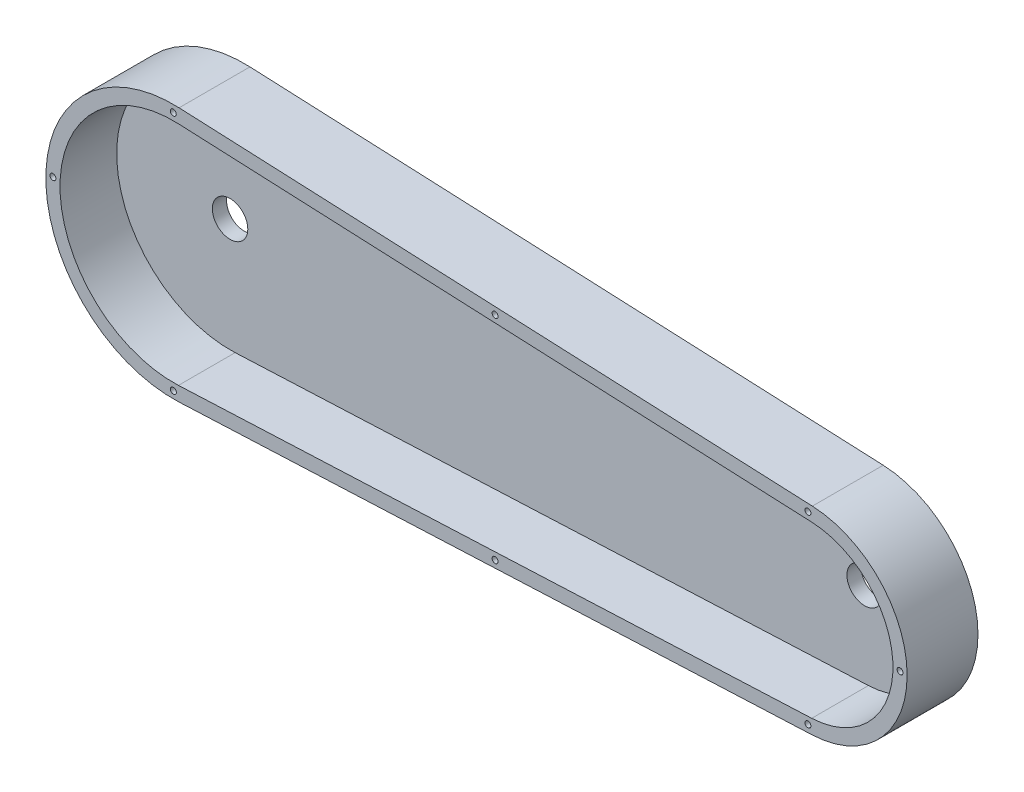
SolidWorks part; units mm, degrees
ref_plane "Front Plane" through (0, 0, 0) normal (0, 0, 1) x (1, 0, 0)
ref_plane "Top Plane" through (0, 0, 0) normal (0, 1, 0) x (1, 0, 0)
ref_plane "Right Plane" through (0, 0, 0) normal (1, 0, 0) x (0, 0, -1)
sketch "Sketch1" plane through (0, 0, 0) normal (0, 0, 1) x (1, 0, 0)
  line L0 (-71.0013, 89.9102) -> (375.8187, 69.9301)
  line L1 (-71.0013, -89.9102) -> (375.8187, -69.9301)
  line L2 (-71.0013, 0) -> (375.8187, 0) construction
  arc A0 (-71.0013, 89.9102) -> (-71.0013, -89.9102) centre (-75.0217, 0) ccw
  arc A1 (375.8187, 69.9301) -> (375.8187, -69.9301) centre (372.6917, 0) cw
  dimension "D1" = 90
  dimension "D2" = 70
  dimension "D3" = 446.82
extrude "Boss-Extrude2" add sketch "Sketch1" along normal blind 50
shell "Shell2" thickness 10
sketch "Sketch2" plane through (0, 0, 10) normal (0, 0, 1) x (1, 0, 0)
  circle A0 centre (-75.0217, 0) radius 12.5
  circle A1 centre (372.6917, 0) radius 12.5
  dimension "D1" = 25
  dimension "D2" = 25
extrude "Cut-Extrude1" cut sketch "Sketch2" against normal blind 10
hole_wizard "M5 Tapped Hole1" positions "Sketch4" profile "Sketch3" tap size "M5" standard "ISO"
sketch "Sketch4" plane through (0, 0, 50) normal (0, 0, 1) x (1, 0, 0)
  line L4 (375.8187, 69.9301) -> (-71.0013, 89.9102) construction
  line L5 (-71.0013, -89.9102) -> (375.8187, -69.9301) construction
  arc A1 (-71.0013, 89.9102) -> (-71.0013, -89.9102) centre (-75.0217, 0) ccw construction
  point P0 (-160.0217, 3.1339)
  point P1 (-75.0813, 85)
  point P3 (-75.0217, -85)
  point P5 (437.6917, 0)
  point P7 (372.6861, -65)
  point P9 (372.6917, 65)
  point P23 (-165.0217, 0)
  point P47 (151.962, 74.9201)
  point P49 (151.9629, -74.9401)
  point P59 (152.4087, 79.9201)
  point P62 (152.4087, -79.9201)
  dimension "D1" = 5
  dimension "D2" = 85
  dimension "D3" = 5
  dimension "D4" = 5
  dimension "D5" = 65
  dimension "D6" = 65
  dimension "D7" = 65
  dimension "D10" = 85
sketch "Sketch3" plane through (-160.0217, 3.1339, 50) normal (1, 0, 0) x (0, -1, 0)
  line L0 (0, 0) -> (0, 11.2618)
  line L1 (0, 11.2618) -> (2.1, 10)
  line L2 (2.1, 10) -> (2.1, 0)
  line L5 (2.1, 0) -> (0, 0)
  line L10 (0, 11.2618) -> (-2.1, 10) construction
  line L11 (0, -6.35) -> (0, 107.95) construction
  dimension "Tap Drill Dia." = 4.2
  dimension "Tap Drill Depth" = 10
  dimension "Drill Angle" = 118
cosmetic thread "Hole Thread1" parameters "D1"=10, "D2"=5
cosmetic thread "Hole Thread2" parameters "D1"=10, "D2"=5
cosmetic thread "Hole Thread3" parameters "D1"=10, "D2"=5
cosmetic thread "Hole Thread4" parameters "D1"=10, "D2"=5
cosmetic thread "Hole Thread5" parameters "D1"=10, "D2"=5
cosmetic thread "Hole Thread6" parameters "D1"=10, "D2"=5
cosmetic thread "Hole Thread7" parameters "D1"=10, "D2"=5
cosmetic thread "Hole Thread8" parameters "D1"=10, "D2"=5
sketch "Sketch5" plane through (0, 0, 0) normal (0, 0, -1) x (-1, 0, 0)
  line L0 (-372.6917, 0) -> (75.0217, 0) construction
sketch "Sketch7" plane through (0, 0, 0) normal (0, 0, -1) x (-1, 0, 0)
  line L0 (-270.4474, 4.605) -> (-111.9727, -17.4354) construction
  line L1 (-268.2215, -5.8009) -> (-109.8269, -27.8301)
  line L2 (-268.2215, -5.8009) -> (-291.6342, -2.5447)
  line L3 (-291.6342, -2.5447) -> (-288.8792, 17.2647)
  line L4 (-288.8792, 17.2647) -> (-90.7858, -10.2858)
  line L5 (-90.7858, -10.2858) -> (-93.5409, -30.0951)
  line L6 (-93.5409, -30.0951) -> (-109.8269, -27.8301)
  circle A0 centre (-270.4474, 4.605) radius 2.5
  circle A1 centre (-191.21, -6.4152) radius 2.5
  circle A2 centre (-111.9727, -17.4354) radius 2.5
  dimension "D5" = 5
  dimension "D6" = 5
  dimension "D7" = 5
  dimension "D1" = 10
  dimension "D2" = 20
  dimension "D3" = 200
  dimension "D4" = 20
extrude "Boss-Extrude3" add sketch "Sketch7" along normal blind 20
cosmetic thread "Cosmetic Thread1" parameters "D2"=6
cosmetic thread "Cosmetic Thread2" parameters "D2"=6
cosmetic thread "Cosmetic Thread3" parameters "D2"=6
